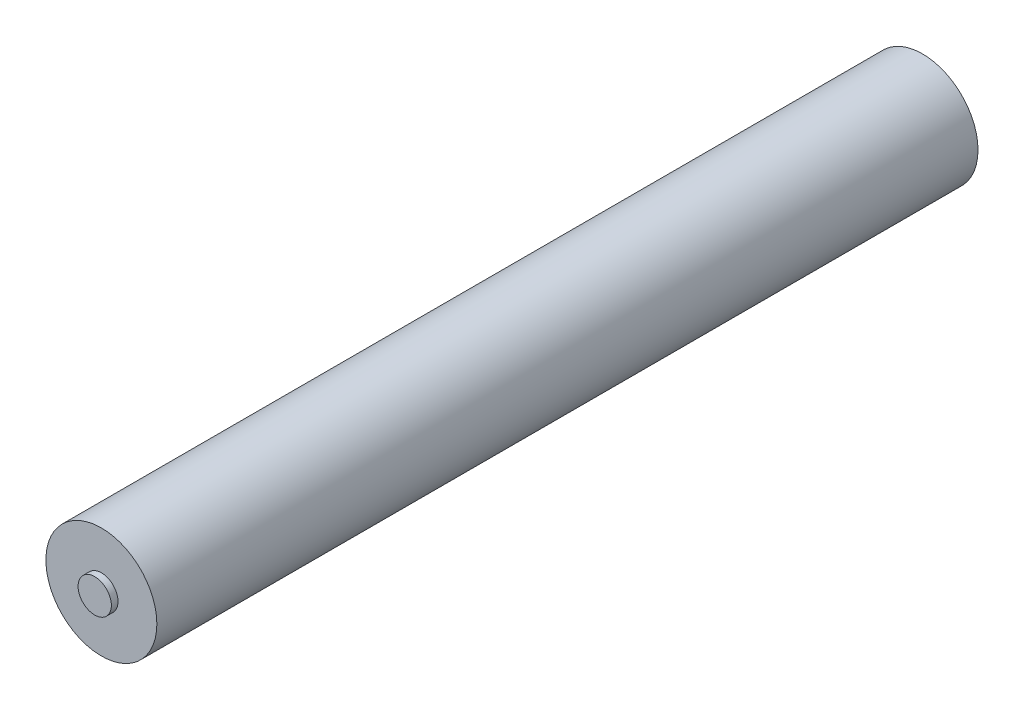
SolidWorks part; units mm, degrees
material "Ferro duttile"
ref_plane "Piano frontale" through (0, 0, 0) normal (0, 0, 1) x (1, 0, 0)
ref_plane "Piano superiore" through (0, 0, 0) normal (0, 1, 0) x (1, 0, 0)
ref_plane "Piano destro" through (0, 0, 0) normal (1, 0, 0) x (0, 0, -1)
sketch "Schizzo1" plane through (0, 0, 0) normal (0, 0, 1) x (1, 0, 0)
  circle A0 centre (0, 0) radius 25
  point P3 (0, 0)
  dimension "D1" = 50
extrude "Estrusione-Estrusione1" add sketch "Schizzo1" along normal blind 370
sketch "Schizzo2" plane through (0, 0, 370) normal (0, 0, 1) x (1, 0, 0)
  circle A0 centre (0, 0) radius 7.5
  dimension "D1" = 15
extrude "Estrusione-Estrusione2" add sketch "Schizzo2" along normal blind 3
